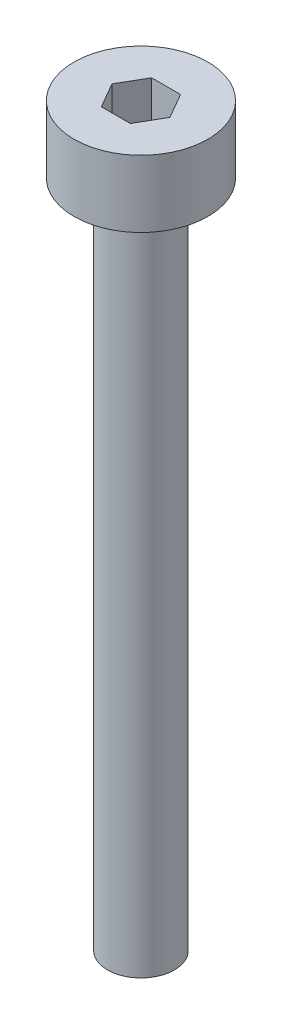
SolidWorks part; units mm, degrees
material "AISI 304"
ref_plane "前视基准面" through (0, 0, 0) normal (0, 0, 1) x (1, 0, 0)
ref_plane "上视基准面" through (0, 0, 0) normal (0, 1, 0) x (1, 0, 0)
ref_plane "右视基准面" through (0, 0, 0) normal (1, 0, 0) x (0, 0, -1)
sketch "草图1" plane through (0, 0, 0) normal (0, 1, 0) x (1, 0, 0)
  circle A0 centre (0, 0) radius 2
  dimension "D1" = 4
extrude "杯头高度" add sketch "草图1" along normal blind 2
sketch "草图2" plane through (0, 2, 0) normal (0, 1, 0) x (1, 0, 0)
  line L1 (0.866, 0) -> (0.433, 0.75)
  line L2 (0.433, 0.75) -> (-0.433, 0.75)
  line L3 (-0.433, 0.75) -> (-0.866, 0)
  line L4 (-0.866, 0) -> (-0.433, -0.75)
  line L5 (-0.433, -0.75) -> (0.433, -0.75)
  line L6 (0.433, -0.75) -> (0.866, 0)
  circle A0 centre (0, 0) radius 0.75 construction
  point P1 (0, 0)
  dimension "D1" = 1.5
extrude "内六角深度" cut sketch "草图2" against normal blind 1.5
sketch "草图3" plane through (0, 0, 0) normal (0, -1, 0) x (1, 0, 0)
  circle A0 centre (0, 0) radius 1
  dimension "D1" = 2
extrude "螺纹长度" add sketch "草图3" along normal blind 20
